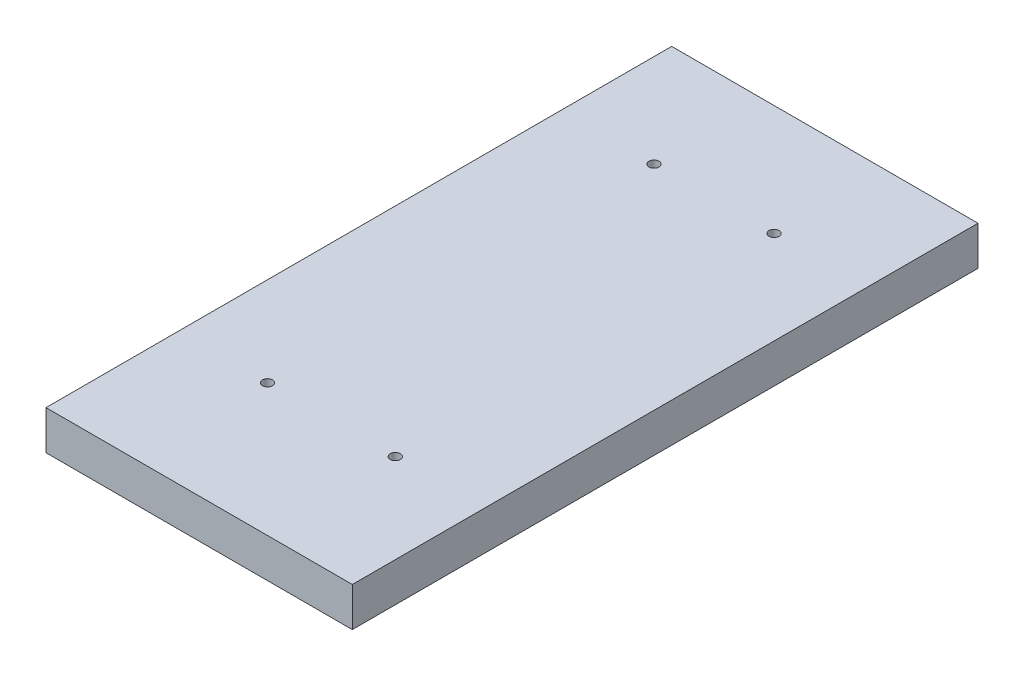
SolidWorks part; units mm, degrees
ref_plane "Front Plane" through (0, 0, 0) normal (0, 0, 1) x (1, 0, 0)
ref_plane "Top Plane" through (0, 0, 0) normal (0, 1, 0) x (1, 0, 0)
ref_plane "Right Plane" through (0, 0, 0) normal (1, 0, 0) x (0, 0, -1)
sketch "Sketch1" plane through (0, 0, 0) normal (0, 1, 0) x (1, 0, 0)
  line L1 (-74.6125, -152.4) -> (74.6125, -152.4)
  line L2 (-74.6125, -152.4) -> (-74.6125, 152.4)
  line L3 (-74.6125, 152.4) -> (74.6125, 152.4)
  line L4 (74.6125, -152.4) -> (74.6125, 152.4)
  line L5 (-74.6125, -152.4) -> (74.6125, 152.4) construction
  line L6 (-74.6125, 152.4) -> (74.6125, -152.4) construction
  point P0 (0, 0)
  dimension "D1" = 149.225
  dimension "D2" = 304.8
extrude "Boss-Extrude1" add sketch "Sketch1" along normal blind 19.05
hole_wizard "#8 Clearance Hole1" positions "Sketch2" profile "Sketch3" hole size "#8" standard "ANSI Inch" end condition through all
sketch "Sketch2" plane through (0, 19.05, 0) normal (0, 1, 0) x (1, 0, 0)
  point P0 (-29.2482, 98.425)
  point P1 (29.2482, 98.425)
sketch "Sketch3" plane through (-29.2482, 19.05, -98.425) normal (1, 0, 0) x (0, 0, 1)
  line L0 (0, 0) -> (0, 19.05)
  line L1 (0, 19.05) -> (2.4574, 19.05)
  line L2 (2.4574, 19.05) -> (2.4574, 0)
  line L3 (2.4574, 0) -> (0, 0)
  line L4 (0, -6.35) -> (0, 107.95) construction
  dimension "Thru Hole Dia." = 4.9149
  dimension "Thru Hole Depth" = 19.05
hole_wizard "#8 Clearance Hole2" positions "Sketch4" profile "Sketch5" hole size "#8" standard "ANSI Inch" end condition through all
sketch "Sketch4" plane through (0, 19.05, 0) normal (0, 1, 0) x (1, 0, 0)
  point P0 (-31.125, -87.9856)
  point P1 (31.125, -87.9856)
  point P3 (0, 0)
sketch "Sketch5" plane through (-31.125, 19.05, 87.9856) normal (1, 0, 0) x (0, 0, 1)
  line L0 (0, 0) -> (0, 19.05)
  line L1 (0, 19.05) -> (2.4574, 19.05)
  line L2 (2.4574, 19.05) -> (2.4574, 0)
  line L5 (2.4574, 0) -> (0, 0)
  line L11 (0, -6.35) -> (0, 107.95) construction
  dimension "Thru Hole Dia." = 4.9149
  dimension "Thru Hole Depth" = 19.05
